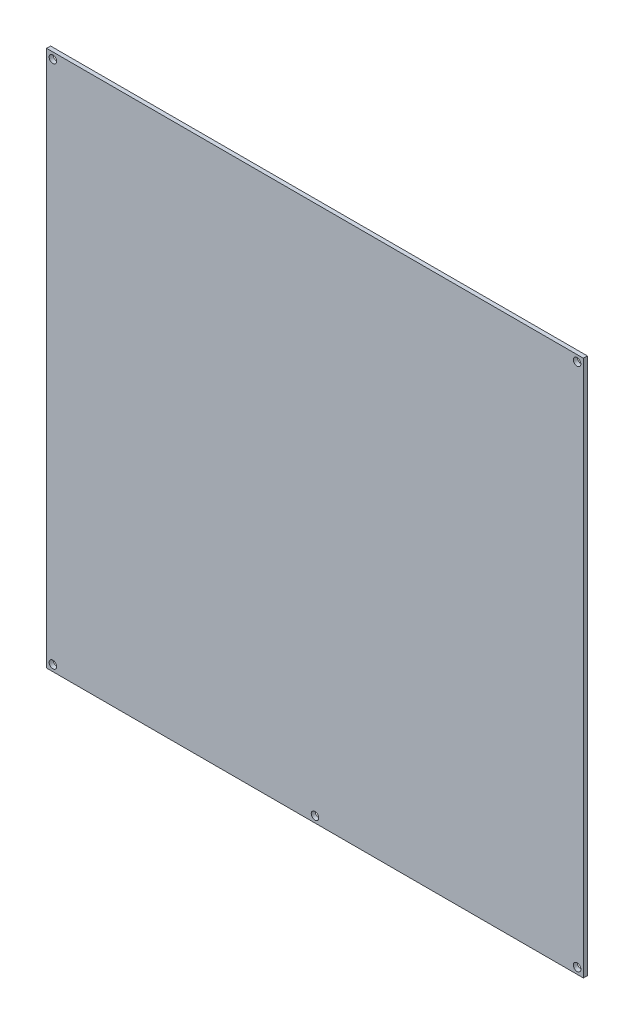
SolidWorks part; units mm, degrees
material "Copper"
ref_plane "Front Plane" through (0, 0, 0) normal (0, 0, 1) x (1, 0, 0)
ref_plane "Top Plane" through (0, 0, 0) normal (0, 1, 0) x (1, 0, 0)
ref_plane "Right Plane" through (0, 0, 0) normal (1, 0, 0) x (0, 0, -1)
sketch "Sketch1" plane through (0, 0, 0) normal (0, 0, 1) x (1, 0, 0)
  line L0 (-100, -100) -> (100, -100) construction
  line L1 (-100, -100) -> (-100, 100) construction
  line L2 (100, -100) -> (100, 100) construction
  line L3 (-100, 100) -> (100, 100) construction
  line L4 (-100, -100) -> (100, 100) construction
  line L5 (100, -100) -> (-100, 100) construction
  line L6 (-107, 0) -> (107, 0) construction
  line L7 (-107, -107) -> (107, -107)
  line L8 (-107, -107) -> (-107, 107)
  line L9 (-107, 107) -> (107, 107)
  line L10 (107, -107) -> (107, 107)
  line L11 (-107, -107) -> (107, 107) construction
  line L12 (-107, 107) -> (107, -107) construction
  circle A0 centre (-104.5, 104.5) radius 1.5
  circle A1 centre (104.5, 104.5) radius 1.5
  circle A2 centre (0, -104.5) radius 1.5
  circle A3 centre (104.5, -104.5) radius 1.5
  circle A4 centre (-104.5, -104.5) radius 1.5
  point P0 (0, 0)
  point P1 (0, 0)
  dimension "D4" = 3
  dimension "D1" = 209
  dimension "D2" = 200
  dimension "D3" = 214
  dimension "D5" = 209
extrude "Boss-Extrude1" add sketch "Sketch1" along normal blind 1.6
